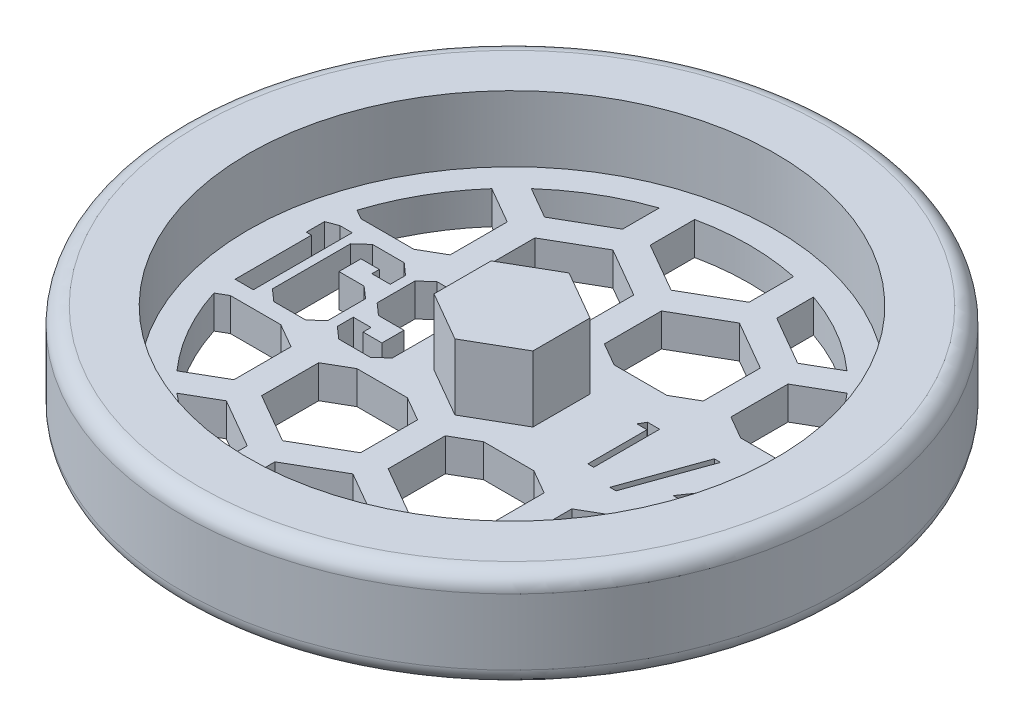
SolidWorks part; units mm, degrees
ref_plane "Front Plane" through (0, 0, 0) normal (0, 0, 1) x (1, 0, 0)
ref_plane "Top Plane" through (0, 0, 0) normal (0, 1, 0) x (1, 0, 0)
ref_plane "Right Plane" through (0, 0, 0) normal (1, 0, 0) x (0, 0, -1)
sketch "Sketch1" plane through (0, 0, 0) normal (0, 0, 1) x (1, 0, 0)
  line L0 (0, 0) -> (30.1625, 0)
  line L1 (31.75, 1.5875) -> (31.75, 7.9375)
  line L2 (30.1625, 9.525) -> (25.4, 9.525)
  line L3 (25.4, 9.525) -> (25.4, 3.175)
  line L4 (25.4, 3.175) -> (0, 3.175)
  line L5 (0, 3.175) -> (0, 0)
  arc A0 (30.1625, 0) -> (31.75, 1.5875) centre (30.1625, 1.5875) ccw
  arc A1 (31.75, 7.9375) -> (30.1625, 9.525) centre (30.1625, 7.9375) ccw
  dimension "D5" = 1.5875
  dimension "D1" = 6.35
  dimension "D2" = 3.175
  dimension "D3" = 25.4
  dimension "D4" = 6.35
revolve "Revolve1" add sketch "Sketch1" angle 360 about L5
sketch "Sketch2" plane through (0, 3.175, 0) normal (0, 1, 0) x (1, 0, 0)
  line L1 (0, -5.4993) -> (4.7625, -2.7496)
  line L2 (4.7625, -2.7496) -> (4.7625, 2.7496)
  line L3 (4.7625, 2.7496) -> (0, 5.4993)
  line L4 (0, 5.4993) -> (-4.7625, 2.7496)
  line L5 (-4.7625, 2.7496) -> (-4.7625, -2.7496)
  line L6 (-4.7625, -2.7496) -> (0, -5.4993)
  circle A0 centre (0, 0) radius 4.7625 construction
  dimension "D1" = 9.525
extrude "Boss-Extrude1" add sketch "Sketch2" along normal blind 6.35
sketch "Sketch3" plane through (0, 3.175, 0) normal (0, 1, 0) x (1, 0, 0)
  line L0 (-4.7625, 0) -> (-25.4, 0) construction
  line L1 (-4.7625, 2.7496) -> (-4.7625, -2.7496) construction
  line L2 (-25.4, -4.7625) -> (-4.7625, -4.7625) construction
  line L3 (4.7625, 0) -> (25.4, 0) construction
  line L4 (4.7625, -2.7496) -> (4.7625, 2.7496) construction
  line L5 (4.7625, -3.175) -> (25.4, -3.175) construction
  circle A0 centre (0, 0) radius 25.4 construction
  circle A1 centre (0, 0) radius 25.4 construction
  text T0 "169" font "Jersey M54" height 9.525
  text T1 "1/4" font "Century Gothic" height 6.35
  dimension "D1" = 4.7625
  dimension "D2" = 3.175
extrude "Cut-Extrude1" cut sketch "Sketch3" against normal through all both and the other way through all
sketch "Sketch4" plane through (0, 3.175, 0) normal (0, 1, 0) x (1, 0, 0)
  line L0 (0, -6.35) -> (0, 6.35)
  line L1 (-21.9604, 6.35) -> (21.9604, 6.35)
  line L2 (-21.9604, -6.35) -> (21.9604, -6.35)
  line L3 (7.4295, -2.7496) -> (12.192, -5.4993)
  line L4 (0, -5.4993) -> (4.7625, -2.7496)
  line L5 (4.7625, -2.7496) -> (4.7625, 2.7496)
  line L6 (4.7625, 2.7496) -> (0, 5.4993)
  line L7 (0, 5.4993) -> (-4.7625, 2.7496)
  line L8 (-4.7625, 2.7496) -> (-4.7625, -2.7496)
  line L9 (-4.7625, -2.7496) -> (0, -5.4993)
  line L10 (6.0325, -4.9493) -> (1.27, -7.699)
  line L11 (1.27, -7.699) -> (1.27, -13.1982)
  line L12 (1.27, -13.1982) -> (6.0325, -15.9479)
  line L13 (6.0325, -15.9479) -> (10.795, -13.1982)
  line L14 (10.795, -13.1982) -> (10.795, -7.699)
  line L15 (10.795, -7.699) -> (6.0325, -4.9493)
  line L16 (7.4295, 2.7496) -> (7.4295, -2.7496)
  line L17 (12.192, 5.4993) -> (7.4295, 2.7496)
  line L18 (16.9545, 2.7496) -> (12.192, 5.4993)
  line L19 (16.9545, -2.7496) -> (16.9545, 2.7496)
  line L20 (12.192, -5.4993) -> (16.9545, -2.7496)
  line L21 (18.2245, -4.9493) -> (13.462, -7.699)
  line L22 (13.462, -7.699) -> (13.462, -13.1982)
  line L23 (13.462, -13.1982) -> (18.2245, -15.9479)
  line L24 (18.2245, -15.9479) -> (22.987, -13.1982)
  line L25 (22.987, -13.1982) -> (22.987, -7.699)
  line L26 (22.987, -7.699) -> (18.2245, -4.9493)
  line L27 (19.6215, -2.7496) -> (24.384, -5.4993)
  line L28 (19.6215, 2.7496) -> (19.6215, -2.7496)
  line L29 (24.384, 5.4993) -> (19.6215, 2.7496)
  line L30 (29.1465, 2.7496) -> (24.384, 5.4993)
  line L31 (29.1465, -2.7496) -> (29.1465, 2.7496)
  line L32 (24.384, -5.4993) -> (29.1465, -2.7496)
  line L33 (30.4165, -4.9493) -> (25.654, -7.699)
  line L34 (25.654, -7.699) -> (25.654, -13.1982)
  line L35 (25.654, -13.1982) -> (30.4165, -15.9479)
  line L36 (30.4165, -15.9479) -> (35.179, -13.1982)
  line L37 (35.179, -13.1982) -> (35.179, -7.699)
  line L38 (35.179, -7.699) -> (30.4165, -4.9493)
  line L39 (-16.9545, -2.7496) -> (-12.192, -5.4993)
  line L40 (-16.9545, 2.7496) -> (-16.9545, -2.7496)
  line L41 (-12.192, 5.4993) -> (-16.9545, 2.7496)
  line L42 (-7.4295, 2.7496) -> (-12.192, 5.4993)
  line L43 (-7.4295, -2.7496) -> (-7.4295, 2.7496)
  line L44 (-12.192, -5.4993) -> (-7.4295, -2.7496)
  line L45 (-6.1595, -4.9493) -> (-10.922, -7.699)
  line L46 (-10.922, -7.699) -> (-10.922, -13.1982)
  line L47 (-10.922, -13.1982) -> (-6.1595, -15.9479)
  line L48 (-6.1595, -15.9479) -> (-1.397, -13.1982)
  line L49 (-1.397, -13.1982) -> (-1.397, -7.699)
  line L50 (-1.397, -7.699) -> (-6.1595, -4.9493)
  line L51 (-29.1465, -2.7496) -> (-24.384, -5.4993)
  line L52 (-29.1465, 2.7496) -> (-29.1465, -2.7496)
  line L53 (-24.384, 5.4993) -> (-29.1465, 2.7496)
  line L54 (-19.6215, 2.7496) -> (-24.384, 5.4993)
  line L55 (-19.6215, -2.7496) -> (-19.6215, 2.7496)
  line L56 (-24.384, -5.4993) -> (-19.6215, -2.7496)
  line L57 (-18.3515, -4.9493) -> (-23.114, -7.699)
  line L58 (-23.114, -7.699) -> (-23.114, -13.1982)
  line L59 (-23.114, -13.1982) -> (-18.3515, -15.9479)
  line L60 (-18.3515, -15.9479) -> (-13.589, -13.1982)
  line L61 (-13.589, -13.1982) -> (-13.589, -7.699)
  line L62 (-13.589, -7.699) -> (-18.3515, -4.9493)
  line L63 (-29.1465, 18.0784) -> (-24.384, 15.3287)
  line L64 (-24.384, 15.3287) -> (-19.6215, 18.0784)
  line L65 (-19.6215, 18.0784) -> (-19.6215, 23.5776)
  line L66 (-19.6215, 23.5776) -> (-24.384, 26.3273)
  line L67 (-24.384, 26.3273) -> (-29.1465, 23.5776)
  line L68 (-29.1465, 23.5776) -> (-29.1465, 18.0784)
  line L69 (-18.3515, 15.8787) -> (-23.114, 13.129)
  line L70 (-23.114, 13.129) -> (-23.114, 7.6298)
  line L71 (-23.114, 7.6298) -> (-18.3515, 4.8801)
  line L72 (-18.3515, 4.8801) -> (-13.589, 7.6298)
  line L73 (-13.589, 7.6298) -> (-13.589, 13.129)
  line L74 (-13.589, 13.129) -> (-18.3515, 15.8787)
  line L75 (-16.9545, 18.0784) -> (-12.192, 15.3287)
  line L76 (-12.192, 15.3287) -> (-7.4295, 18.0784)
  line L77 (-7.4295, 18.0784) -> (-7.4295, 23.5776)
  line L78 (-7.4295, 23.5776) -> (-12.192, 26.3273)
  line L79 (-12.192, 26.3273) -> (-16.9545, 23.5776)
  line L80 (-16.9545, 23.5776) -> (-16.9545, 18.0784)
  line L81 (-6.1595, 15.8787) -> (-10.922, 13.129)
  line L82 (-10.922, 13.129) -> (-10.922, 7.6298)
  line L83 (-10.922, 7.6298) -> (-6.1595, 4.8801)
  line L84 (-6.1595, 4.8801) -> (-1.397, 7.6298)
  line L85 (-1.397, 7.6298) -> (-1.397, 13.129)
  line L86 (-1.397, 13.129) -> (-6.1595, 15.8787)
  line L87 (6.0325, 15.8787) -> (1.27, 13.129)
  line L88 (1.27, 13.129) -> (1.27, 7.6298)
  line L89 (1.27, 7.6298) -> (6.0325, 4.8801)
  line L90 (6.0325, 4.8801) -> (10.795, 7.6298)
  line L91 (10.795, 7.6298) -> (10.795, 13.129)
  line L92 (10.795, 13.129) -> (6.0325, 15.8787)
  line L93 (-4.7625, 18.0784) -> (0, 15.3287)
  line L94 (-4.7625, 23.5776) -> (-4.7625, 18.0784)
  line L95 (0, 26.3273) -> (-4.7625, 23.5776)
  line L96 (4.7625, 23.5776) -> (0, 26.3273)
  line L97 (4.7625, 18.0784) -> (4.7625, 23.5776)
  line L98 (0, 15.3287) -> (4.7625, 18.0784)
  line L99 (7.4295, 18.0784) -> (12.192, 15.3287)
  line L100 (12.192, 15.3287) -> (16.9545, 18.0784)
  line L101 (16.9545, 18.0784) -> (16.9545, 23.5776)
  line L102 (16.9545, 23.5776) -> (12.192, 26.3273)
  line L103 (12.192, 26.3273) -> (7.4295, 23.5776)
  line L104 (7.4295, 23.5776) -> (7.4295, 18.0784)
  line L105 (19.6215, 18.0784) -> (24.384, 15.3287)
  line L106 (24.384, 15.3287) -> (29.1465, 18.0784)
  line L107 (29.1465, 18.0784) -> (29.1465, 23.5776)
  line L108 (29.1465, 23.5776) -> (24.384, 26.3273)
  line L109 (24.384, 26.3273) -> (19.6215, 23.5776)
  line L110 (19.6215, 23.5776) -> (19.6215, 18.0784)
  line L111 (18.2245, 15.8787) -> (13.462, 13.129)
  line L112 (13.462, 13.129) -> (13.462, 7.6298)
  line L113 (13.462, 7.6298) -> (18.2245, 4.8801)
  line L114 (18.2245, 4.8801) -> (22.987, 7.6298)
  line L115 (22.987, 7.6298) -> (22.987, 13.129)
  line L116 (22.987, 13.129) -> (18.2245, 15.8787)
  line L117 (30.4165, 15.8787) -> (25.654, 13.129)
  line L118 (25.654, 13.129) -> (25.654, 7.6298)
  line L119 (25.654, 7.6298) -> (30.4165, 4.8801)
  line L120 (30.4165, 4.8801) -> (35.179, 7.6298)
  line L121 (35.179, 7.6298) -> (35.179, 13.129)
  line L122 (35.179, 13.129) -> (30.4165, 15.8787)
  line L123 (-29.1465, -23.5776) -> (-24.384, -26.3273)
  line L124 (-24.384, -26.3273) -> (-19.6215, -23.5776)
  line L125 (-19.6215, -23.5776) -> (-19.6215, -18.0784)
  line L126 (-19.6215, -18.0784) -> (-24.384, -15.3287)
  line L127 (-24.384, -15.3287) -> (-29.1465, -18.0784)
  line L128 (-29.1465, -18.0784) -> (-29.1465, -23.5776)
  line L129 (-18.3515, -25.7773) -> (-23.114, -28.527)
  line L130 (-23.114, -28.527) -> (-23.114, -34.0262)
  line L131 (-23.114, -34.0262) -> (-18.3515, -36.7759)
  line L132 (-18.3515, -36.7759) -> (-13.589, -34.0262)
  line L133 (-13.589, -34.0262) -> (-13.589, -28.527)
  line L134 (-13.589, -28.527) -> (-18.3515, -25.7773)
  line L135 (-16.9545, -23.5776) -> (-12.192, -26.3273)
  line L136 (-12.192, -26.3273) -> (-7.4295, -23.5776)
  line L137 (-7.4295, -23.5776) -> (-7.4295, -18.0784)
  line L138 (-7.4295, -18.0784) -> (-12.192, -15.3287)
  line L139 (-12.192, -15.3287) -> (-16.9545, -18.0784)
  line L140 (-16.9545, -18.0784) -> (-16.9545, -23.5776)
  line L141 (-6.1595, -25.7773) -> (-10.922, -28.527)
  line L142 (-10.922, -28.527) -> (-10.922, -34.0262)
  line L143 (-10.922, -34.0262) -> (-6.1595, -36.7759)
  line L144 (-6.1595, -36.7759) -> (-1.397, -34.0262)
  line L145 (-1.397, -34.0262) -> (-1.397, -28.527)
  line L146 (-1.397, -28.527) -> (-6.1595, -25.7773)
  line L147 (6.0325, -25.7773) -> (1.27, -28.527)
  line L148 (1.27, -28.527) -> (1.27, -34.0262)
  line L149 (1.27, -34.0262) -> (6.0325, -36.7759)
  line L150 (6.0325, -36.7759) -> (10.795, -34.0262)
  line L151 (10.795, -34.0262) -> (10.795, -28.527)
  line L152 (10.795, -28.527) -> (6.0325, -25.7773)
  line L153 (-4.7625, -23.5776) -> (0, -26.3273)
  line L154 (-4.7625, -18.0784) -> (-4.7625, -23.5776)
  line L155 (0, -15.3287) -> (-4.7625, -18.0784)
  line L156 (4.7625, -18.0784) -> (0, -15.3287)
  line L157 (4.7625, -23.5776) -> (4.7625, -18.0784)
  line L158 (0, -26.3273) -> (4.7625, -23.5776)
  line L159 (7.4295, -23.5776) -> (12.192, -26.3273)
  line L160 (12.192, -26.3273) -> (16.9545, -23.5776)
  line L161 (16.9545, -23.5776) -> (16.9545, -18.0784)
  line L162 (16.9545, -18.0784) -> (12.192, -15.3287)
  line L163 (12.192, -15.3287) -> (7.4295, -18.0784)
  line L164 (7.4295, -18.0784) -> (7.4295, -23.5776)
  line L165 (19.6215, -23.5776) -> (24.384, -26.3273)
  line L166 (24.384, -26.3273) -> (29.1465, -23.5776)
  line L167 (29.1465, -23.5776) -> (29.1465, -18.0784)
  line L168 (29.1465, -18.0784) -> (24.384, -15.3287)
  line L169 (24.384, -15.3287) -> (19.6215, -18.0784)
  line L170 (19.6215, -18.0784) -> (19.6215, -23.5776)
  line L171 (18.2245, -25.7773) -> (13.462, -28.527)
  line L172 (13.462, -28.527) -> (13.462, -34.0262)
  line L173 (13.462, -34.0262) -> (18.2245, -36.7759)
  line L174 (18.2245, -36.7759) -> (22.987, -34.0262)
  line L175 (22.987, -34.0262) -> (22.987, -28.527)
  line L176 (22.987, -28.527) -> (18.2245, -25.7773)
  line L177 (30.4165, -25.7773) -> (25.654, -28.527)
  line L178 (25.654, -28.527) -> (25.654, -34.0262)
  line L179 (25.654, -34.0262) -> (30.4165, -36.7759)
  line L180 (30.4165, -36.7759) -> (35.179, -34.0262)
  line L181 (35.179, -34.0262) -> (35.179, -28.527)
  line L182 (35.179, -28.527) -> (30.4165, -25.7773)
  circle A0 centre (0, 0) radius 22.86
  circle A1 centre (0, 0) radius 4.7625 construction
  circle A2 centre (6.0325, -10.4486) radius 4.7625 construction
  point P6 (0, 0)
  point P9 (0, 6.35)
  point P12 (0, -6.35)
  dimension "D1" = 45.72
  dimension "D2" = 12.7
  dimension "D3" = 9.525
  dimension "D4" = 9.525
  dimension "D5" = 2.54
  dimension "D6" = 1.27
  dimension "D9" = 2.1997
  dimension "D7" = 3
  dimension "D8" = 3
  dimension "D10" = 2
  dimension "D11" = 2
extrude "Cut-Extrude3" cut sketch "Sketch4" against normal through all both and the other way through all contours L74 A0 L71 L1 L72 L73 | L77 A0 L75 L76 | L85 L86 L81 L82 L83 L1 L84 | L97 A0 L94 L93 L98 | L91 L92 L87 L88 L89 L1 L90 | L100 A0 L104 L99 | L114 A0 L111 L112 L113 L1 | L23 A0 L26 L2 L21 L22 | L164 A0 L162 L163 | L14 L15 L2 L10 L11 L12 L13 | L154 A0 L157 L156 L155 | L49 L50 L2 L45 L46 L47 L48 | L139 A0 L137 L138 | L57 A0 L60 L61 L62 L2
